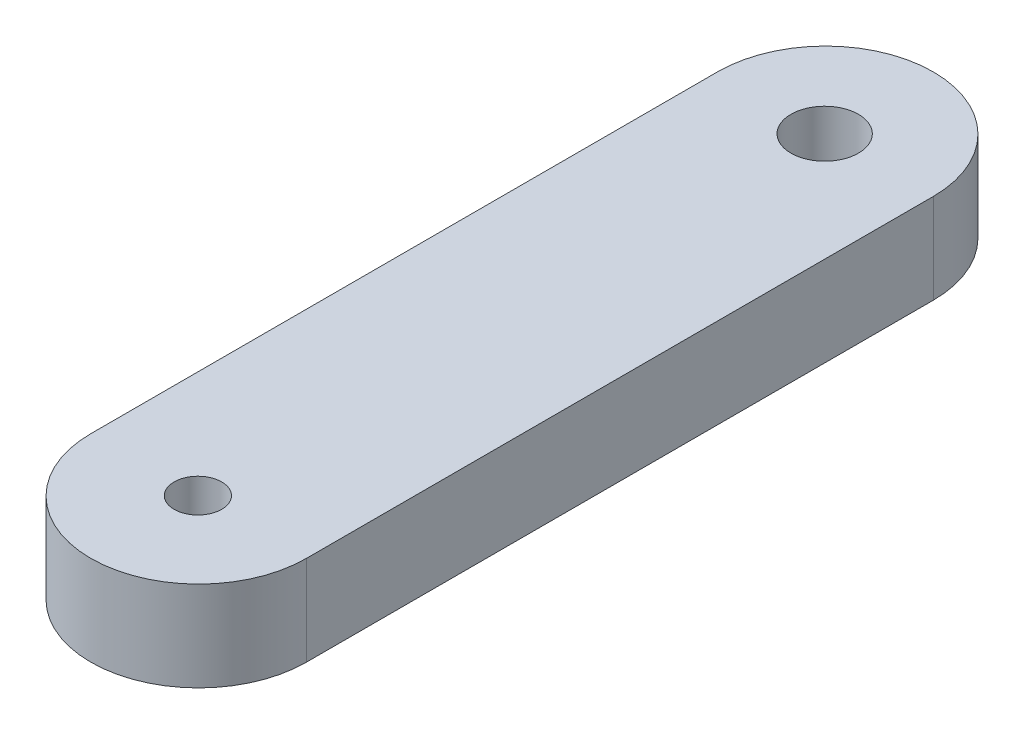
SolidWorks part; units mm, degrees
ref_plane "Front Plane" through (0, 0, 0) normal (0, 0, 1) x (1, 0, 0)
ref_plane "Top Plane" through (0, 0, 0) normal (0, 1, 0) x (1, 0, 0)
ref_plane "Right Plane" through (0, 0, 0) normal (1, 0, 0) x (0, 0, -1)
sketch "Sketch1" plane through (0, 0, 0) normal (0, 1, 0) x (1, 0, 0)
  line L0 (-3.7849, 0) -> (-3.7849, 22.1335)
  line L3 (3.8351, 22.1335) -> (3.8351, 0)
  circle A0 centre (0, 22.1335) radius 1.1906
  circle A1 centre (0, 0) radius 0.8401
  arc A2 (-3.7849, 22.1335) -> (3.8351, 22.1335) centre (0.0251, 22.1335) cw
  arc A3 (3.8351, 0) -> (-3.7849, 0) centre (0.0251, 0) cw
  dimension "D1" = 2.3813
  dimension "D3" = 3.81
  dimension "D4" = 1.6802
  dimension "D2" = 22.1335
extrude "Boss-Extrude1" add sketch "Sketch1" along normal blind 3.175
